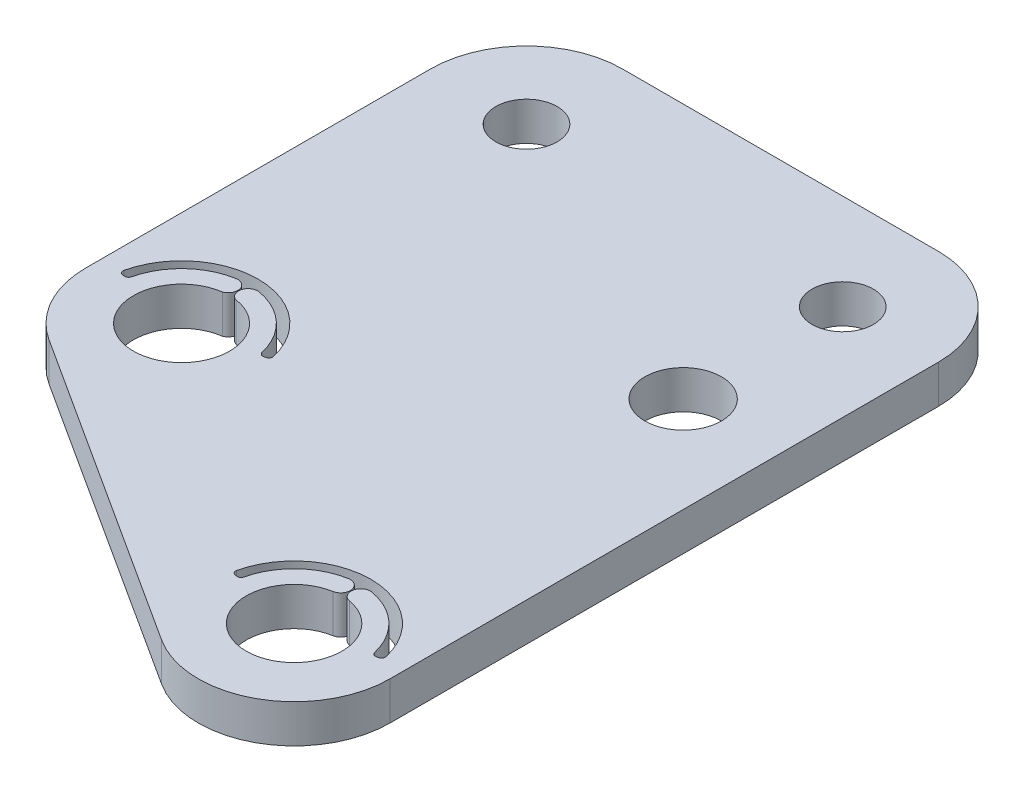
SolidWorks part; units mm, degrees
ref_plane "Front" through (0, 0, 0) normal (0, 0, 1) x (1, 0, 0)
ref_plane "Top" through (0, 0, 0) normal (0, 1, 0) x (1, 0, 0)
ref_plane "Right" through (0, 0, 0) normal (1, 0, 0) x (0, 0, -1)
sketch "Sketch1" plane through (0, 0, 0) normal (0, 1, 0) x (1, 0, 0)
  line L0 (0, 0) -> (26.5, 0)
  line L1 (26.5, 0) -> (26.5, -42.7917)
  line L2 (26.5, -42.7917) -> (0, -25.7273)
  line L3 (0, -25.7273) -> (0, 0)
  line L4 (5, -5) -> (21.5, -5) construction
  line L5 (21.5, -5) -> (21.5, -33.625) construction
  line L6 (21.5, -33.625) -> (5, -23) construction
  line L7 (5, -23) -> (5, -5) construction
  circle A0 centre (5, -23) radius 2.51
  circle A1 centre (21.5, -33.625) radius 2.5
  circle A2 centre (21.5, -5) radius 1.6
  circle A3 centre (5, -5) radius 1.6
  circle A4 centre (21.5, -13.325) radius 2
  dimension "D8" = 5.02
  dimension "D9" = 3.2
  dimension "D10" = 5
  dimension "D12" = 4
  dimension "D1" = 16.5
  dimension "D3" = 5
  dimension "D4" = 5
  dimension "D5" = 5
  dimension "D6" = 5
  dimension "D7" = 18
  dimension "D2" = 10.625
  dimension "D11" = 8.325
extrude "Boss-Extrude1" add sketch "Sketch1" along normal blind 2
fillet "Fillet1" radius 5 4 edges at (26.5, 1, 0) (0, 1, 0) (0, 1, 25.7273) (26.5, 1, 42.7917)
other "Move Face1" [suppressed] parameters "D1"=0.0762
sketch "Sketch2" plane through (0, 2, 0) normal (0, 1, 0) x (1, 0, 0)
  line B0 (17.8615, -32.9834) -> (17.7629, -32.9661)
  line B1 (25.1385, -32.9834) -> (25.2371, -32.9661)
  line B2 (20.9791, -30.6706) -> (21.5, -33.625) construction
  arc B3 (17.6028, -32.724) -> (25.3972, -32.724) centre (21.5, -33.625) cw
  arc B4 (21.0659, -31.163) -> (20.8922, -30.1782) centre (20.9791, -30.6706) ccw
  arc B5 (20.8922, -30.1782) -> (18.0911, -32.8318) centre (21.5, -33.625) ccw
  arc B6 (22.1078, -30.1782) -> (24.9089, -32.8318) centre (21.5, -33.625) cw
  arc B7 (21.9341, -31.163) -> (22.1078, -30.1782) centre (22.0209, -30.6706) cw
  arc B8 (21.0659, -31.163) -> (21.9341, -31.163) centre (21.5, -33.625) cw
  arc B9 (17.8615, -32.9834) -> (18.0911, -32.8318) centre (17.8963, -32.7865) ccw
  arc B10 (17.7629, -32.9661) -> (17.6028, -32.724) centre (17.7976, -32.7691) cw
  arc B11 (25.2371, -32.9661) -> (25.3972, -32.724) centre (25.2024, -32.7691) ccw
  arc B12 (25.1385, -32.9834) -> (24.9089, -32.8318) centre (25.1037, -32.7865) cw
  line B13 (1.3615, -22.3584) -> (1.2629, -22.3411)
  line B14 (8.6385, -22.3584) -> (8.7371, -22.3411)
  line B15 (4.4791, -20.0456) -> (5, -23) construction
  arc B16 (1.1028, -22.099) -> (8.8972, -22.099) centre (5, -23) cw
  arc B17 (4.5659, -20.538) -> (4.3922, -19.5532) centre (4.4791, -20.0456) ccw
  arc B18 (4.3922, -19.5532) -> (1.5911, -22.2068) centre (5, -23) ccw
  arc B19 (5.6078, -19.5532) -> (8.4089, -22.2068) centre (5, -23) cw
  arc B20 (5.4341, -20.538) -> (5.6078, -19.5532) centre (5.5209, -20.0456) cw
  arc B21 (4.5659, -20.538) -> (5.4341, -20.538) centre (5, -23) cw
  arc B22 (1.3615, -22.3584) -> (1.5911, -22.2068) centre (1.3963, -22.1615) ccw
  arc B23 (1.2629, -22.3411) -> (1.1028, -22.099) centre (1.2976, -22.1441) cw
  arc B24 (8.7371, -22.3411) -> (8.8972, -22.099) centre (8.7024, -22.1441) ccw
  arc B25 (8.6385, -22.3584) -> (8.4089, -22.2068) centre (8.6037, -22.1615) cw
sketch_block_instance "5mm_bore_flexure_relief-1"
sketch_block "5mm_bore_flexure_relief" parameters "D4"=2.5, "D6"=0.2, "D1"=80, "D2"=0.5, "D3"=70, "D5"=1
sketch_block_instance "5mm_bore_flexure_relief-2"
extrude "Cut-Extrude2" cut sketch "Sketch2" against normal through all
sketch "Sketch3" plane through (0, 0, 0) normal (0, 0, -1) x (-1, 0, 0)
  line L0 (-21.5, 0.4) -> (-5, 0.4) construction
  line L1 (-21.5, 2) -> (-21.5, 0) construction
  line L2 (-5, 0) -> (-5, 2) construction
  line L3 (-21.5, 0) -> (-5, 0) construction
  text T0 "MRP-01" font "Century Gothic" height in points 5
  dimension "D1" = 0.4
extrude "Cut-Extrude3" cut sketch "Sketch3" against normal blind 0.4
equation "\"D4@Sketch1\"=\"D3@Sketch1\""
equation "\"D5@Sketch1\"=\"D3@Sketch1\""
equation "\"D6@Sketch1\"=\"D3@Sketch1\""
